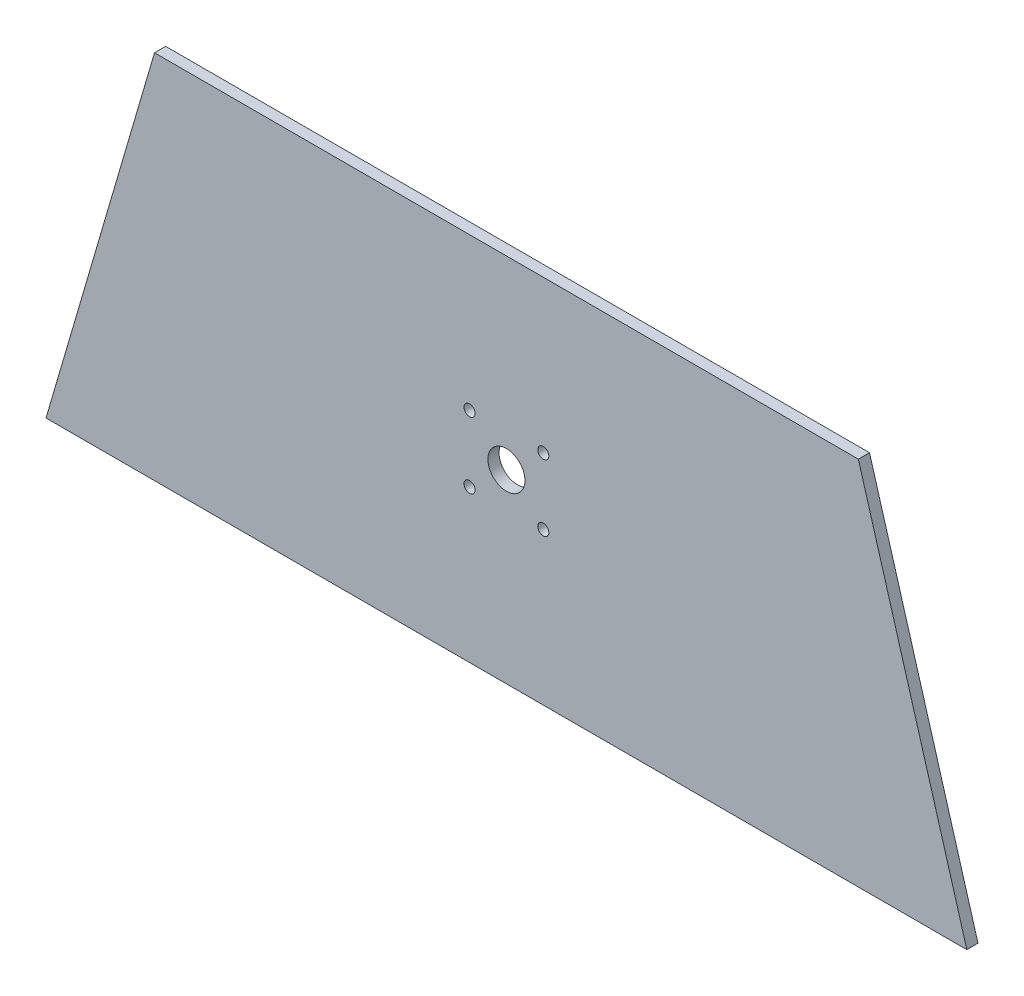
SolidWorks part; units mm, degrees
ref_plane "Front Plane" through (0, 0, 0) normal (0, 0, 1) x (1, 0, 0)
ref_plane "Top Plane" through (0, 0, 0) normal (0, 1, 0) x (1, 0, 0)
ref_plane "Right Plane" through (0, 0, 0) normal (1, 0, 0) x (0, 0, -1)
sketch "Sketch1" plane through (0, 0, 0) normal (0, 0, 1) x (1, 0, 0)
  line L0 (-3.5, 0) -> (245, 0)
  line L3 (149.129, 0) -> (149.129, 100) construction
  line L5 (-3.5, 0) -> (25.7799, 100)
  line L6 (245, 0) -> (215.7201, 100)
  line L7 (25.7799, 100) -> (215.7201, 100)
extrude "Boss-Extrude1" add sketch "Sketch1" along normal blind 3 and the other way blind 0.0067
hole_wizard "Ø10.0mm Dowel Hole1" positions "Sketch2" profile "Sketch3" hole size "Ø10.0" standard "ANSI Metric" end condition up to next
sketch "Sketch2" plane through (0, 0, 3) normal (0, 0, 1) x (1, 0, 0)
  point P0 (120.75, 50)
sketch "Sketch3" plane through (120.75, 50, 3) normal (1, 0, 0) x (0, -1, 0)
  line L0 (0, 0) -> (0, 3.0067)
  line L1 (0, 3.0067) -> (5, 3.0067)
  line L2 (5, 3.0067) -> (5, 0)
  line L5 (5, 0) -> (0, 0)
  line L11 (0, -6.35) -> (0, 107.95) construction
  dimension "Thru Hole Dia." = 10
  dimension "Thru Hole Depth" = 3.0067
hole_wizard "Ø3.0mm Dowel Hole1" positions "Sketch4" profile "Sketch5" hole size "Ø3.0" standard "ANSI Metric" end condition up to next
sketch "Sketch4" plane through (0, 0, 3) normal (0, 0, 1) x (1, 0, 0)
  point P0 (110.8, 58.95)
  point P3 (130.7, 58.95)
  point P6 (130.7, 41.05)
  point P9 (110.8, 41.05)
sketch "Sketch5" plane through (110.8, 58.95, 3) normal (1, 0, 0) x (0, -1, 0)
  line L0 (0, 0) -> (0, 3.0067)
  line L1 (0, 3.0067) -> (1.5, 3.0067)
  line L2 (1.5, 3.0067) -> (1.5, 0)
  line L5 (1.5, 0) -> (0, 0)
  line L11 (0, -6.35) -> (0, 107.95) construction
  dimension "Thru Hole Dia." = 3
  dimension "Thru Hole Depth" = 3.0067
